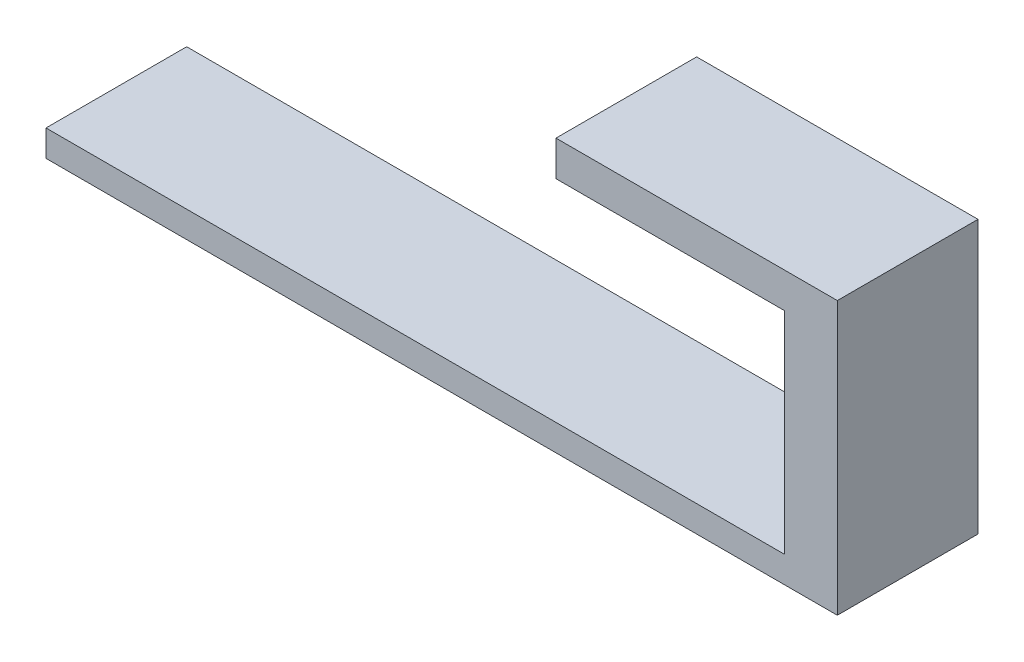
SolidWorks part; units mm, degrees
ref_plane "Front Plane" through (0, 0, 0) normal (0, 0, 1) x (1, 0, 0)
ref_plane "Top Plane" through (0, 0, 0) normal (0, 1, 0) x (1, 0, 0)
ref_plane "Right Plane" through (0, 0, 0) normal (1, 0, 0) x (0, 0, -1)
sketch "Sketch1" plane through (0, 0, 0) normal (0, 1, 0) x (1, 0, 0)
  line L1 (-22.5, -4) -> (22.5, -4)
  line L2 (-22.5, -4) -> (-22.5, 4)
  line L3 (-22.5, 4) -> (22.5, 4)
  line L4 (22.5, -4) -> (22.5, 4)
  line L5 (-22.5, -4) -> (22.5, 4) construction
  line L6 (-22.5, 4) -> (22.5, -4) construction
  point P0 (0, 0)
  dimension "D1" = 8
  dimension "D2" = 45
extrude "Boss-Extrude1" add sketch "Sketch1" along normal blind 1.5
sketch "Sketch2" plane through (0, 1.5, 0) normal (0, 1, 0) x (1, 0, 0)
  line L0 (-22.5, -4) -> (22.5, -4) construction
  line L1 (22.5, 4) -> (19.5, 4)
  line L2 (22.5, 4) -> (22.5, -4)
  line L3 (22.5, -4) -> (19.5, -4)
  line L4 (19.5, 4) -> (19.5, -4)
  dimension "D1" = 3
extrude "Boss-Extrude2" add sketch "Sketch2" along normal blind 14
sketch "Sketch3" plane through (19.5, 0, 0) normal (-1, 0, 0) x (0, 0, 1)
  line L0 (4, 15.5) -> (4, 1.5) construction
  line L1 (-4, 15.5) -> (4, 15.5)
  line L2 (-4, 15.5) -> (-4, 13.5)
  line L3 (-4, 13.5) -> (4, 13.5)
  line L4 (4, 15.5) -> (4, 13.5)
  dimension "D1" = 2
extrude "Boss-Extrude3" add sketch "Sketch3" along normal blind 13
